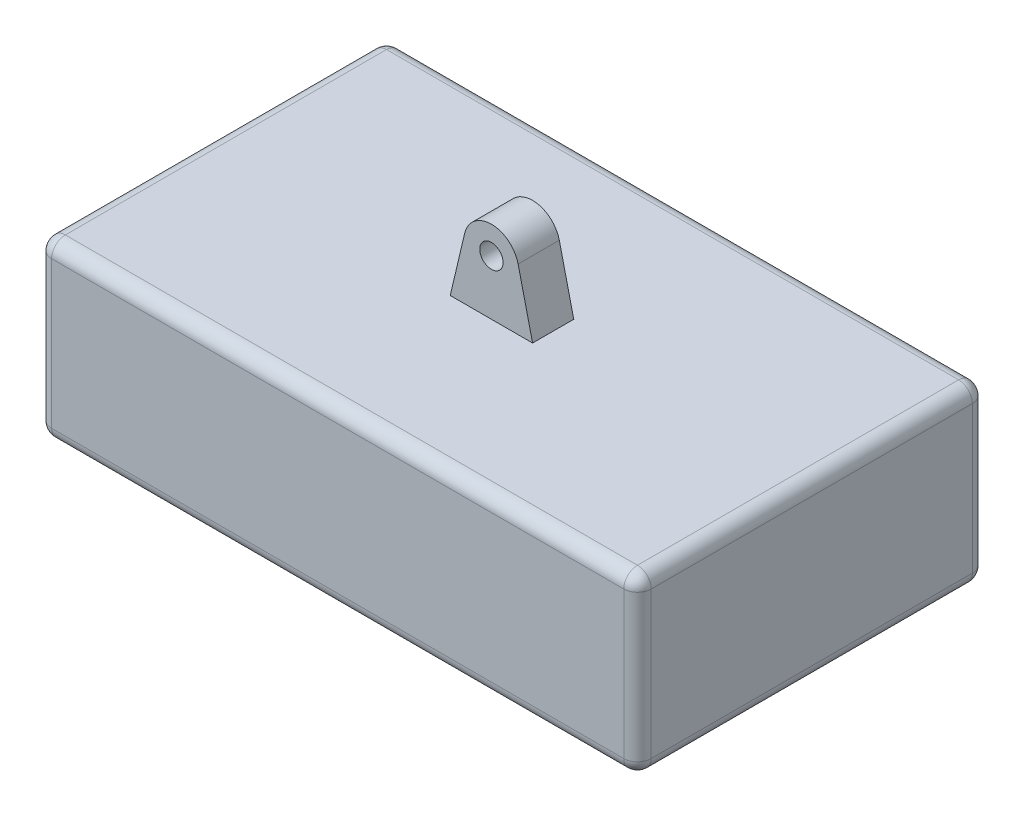
SolidWorks part; units mm, degrees
ref_plane "Front Plane" through (0, 0, 0) normal (0, 0, 1) x (1, 0, 0)
ref_plane "Top Plane" through (0, 0, 0) normal (0, 1, 0) x (1, 0, 0)
ref_plane "Right Plane" through (0, 0, 0) normal (1, 0, 0) x (0, 0, -1)
sketch "Sketch1" plane through (0, 0, 0) normal (0, 1, 0) x (1, 0, 0)
  line L1 (109.22, 63.5) -> (-109.22, 63.5)
  line L2 (109.22, 63.5) -> (109.22, -63.5)
  line L3 (109.22, -63.5) -> (-109.22, -63.5)
  line L4 (-109.22, 63.5) -> (-109.22, -63.5)
  line L5 (109.22, 63.5) -> (-109.22, -63.5) construction
  line L6 (109.22, -63.5) -> (-109.22, 63.5) construction
  point P0 (0, 0)
  dimension "D1" = 218.44
  dimension "D2" = 127
extrude "Boss-Extrude1" add sketch "Sketch1" along normal blind 63.5
sketch "Sketch2" plane through (0, 63.5, 0) normal (0, 1, 0) x (1, 0, 0)
  line L1 (-15, 7.5) -> (15, 7.5)
  line L2 (-15, 7.5) -> (-15, -7.5)
  line L3 (-15, -7.5) -> (15, -7.5)
  line L4 (15, 7.5) -> (15, -7.5)
  line L5 (-15, 7.5) -> (15, -7.5) construction
  line L6 (-15, -7.5) -> (15, 7.5) construction
  point P0 (0, 0)
  dimension "D1" = 15
  dimension "D2" = 30
extrude "Boss-Extrude2" add sketch "Sketch2" along normal blind 30
sketch "Sketch3" plane through (0, 0, -7.5) normal (0, 0, -1) x (-1, 0, 0)
  line L0 (0, 93.5) -> (0, 63.5) construction
  line L1 (-15, 93.5) -> (15, 93.5) construction
  line L2 (-109.22, 63.5) -> (109.22, 63.5) construction
  line L3 (-15, 63.5) -> (-9.7321, 85.7991)
  line L4 (15, 63.5) -> (9.7321, 85.7991)
  circle A0 centre (0, 83.5) radius 10
  circle A1 centre (0, 83.5) radius 4.25
  line M4 (15, 63.5) -> (15, 93.5)
  line M5 (15, 93.5) -> (-15, 93.5)
  line M6 (-15, 93.5) -> (-15, 63.5)
  dimension "D1" = 20
  dimension "D2" = 8.5
extrude "Cut-Extrude1" cut sketch "Sketch3" against normal up to next contours L0 A1 | A1 L0 | A0 L4 M4 M5 | A0 L3 M5 M6
fillet "Fillet1" radius 5 12 edges at (0, 0, 63.5) (109.22, 0, 0) (0, 0, -63.5) (-109.22, 0, 0) (0, 63.5, 63.5) (109.22, 63.5, 0) (0, 63.5, -63.5) (-109.22, 63.5, 0) (109.22, 31.75, -63.5) (109.22, 31.75, 63.5) (-109.22, 31.75, 63.5) (-109.22, 31.75, -63.5)
